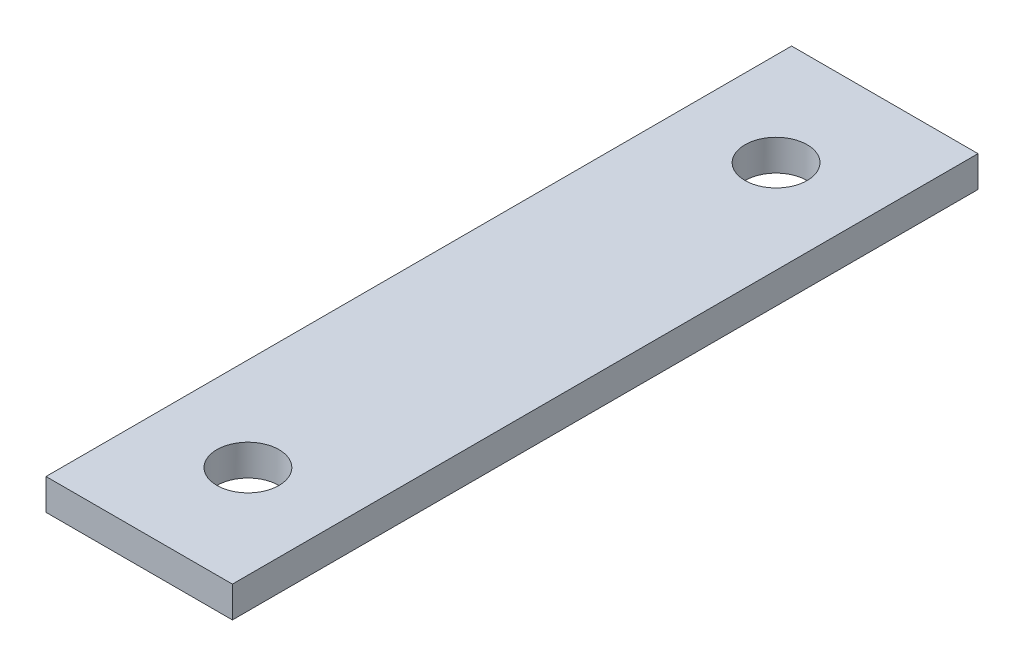
SolidWorks part; units mm, degrees
material "1060 Alloy"
ref_plane "Front" through (0, 0, 0) normal (0, 0, 1) x (1, 0, 0)
ref_plane "Top" through (0, 0, 0) normal (0, 1, 0) x (1, 0, 0)
ref_plane "Right" through (0, 0, 0) normal (1, 0, 0) x (0, 0, -1)
sketch "Sketch1" plane through (0, 0, 0) normal (0, 1, 0) x (1, 0, 0)
  line L1 (-1.5, -3.2318) -> (1.5, -3.2318)
  line L2 (-1.5, -3.2318) -> (-1.5, 8.7682)
  line L3 (-1.5, 8.7682) -> (1.5, 8.7682)
  line L4 (1.5, -3.2318) -> (1.5, 8.7682)
  line L5 (-1.5, -3.2318) -> (1.5, 8.7682) construction
  line L6 (-1.5, 8.7682) -> (1.5, -3.2318) construction
  point P0 (0, 0)
  dimension "D1" = 3
  dimension "D2" = 12
extrude "Boss-Extrude1" add sketch "Sketch1" along normal blind 0.5
sketch "Sketch2" plane through (0, 0.5, 0) normal (0, 1, 0) x (1, 0, 0)
  line L0 (-1.5, -3.2318) -> (1.5, -3.2318) construction
  line L1 (1.5, 8.7682) -> (-1.5, 8.7682) construction
  circle A0 centre (0, 7.0182) radius 0.5
  circle A1 centre (0, -1.4818) radius 0.5
  dimension "D1" = 1
  dimension "D2" = 1
  dimension "D3" = 1.75
  dimension "D4" = 1.75
  dimension "D5" = 1.5
  dimension "D6" = 1.5
extrude "Cut-Extrude1" cut sketch "Sketch2" against normal blind 1
